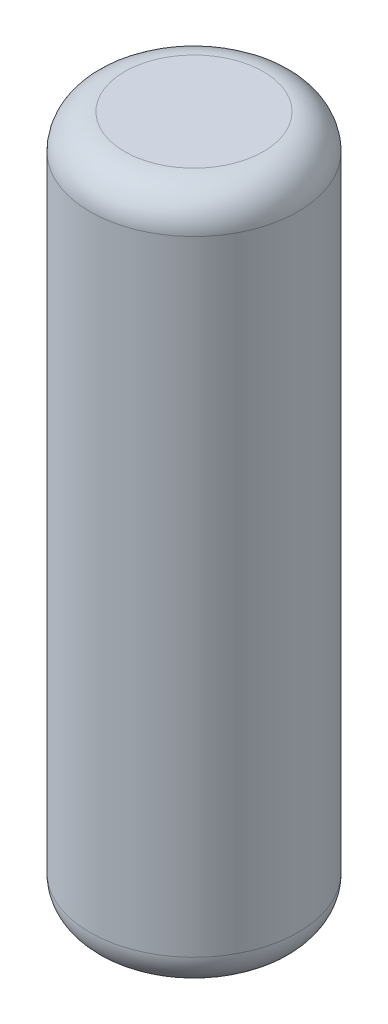
SolidWorks part; units mm, degrees
material "Cast Alloy Steel"
ref_plane "Front Plane" through (0, 0, 0) normal (0, 0, 1) x (1, 0, 0)
ref_plane "Top Plane" through (0, 0, 0) normal (0, 1, 0) x (1, 0, 0)
ref_plane "Right Plane" through (0, 0, 0) normal (1, 0, 0) x (0, 0, -1)
sketch "Sketch1" plane through (0, 0, 0) normal (0, 1, 0) x (1, 0, 0)
  circle A0 centre (0, 0) radius 30
  dimension "D1" = 60
extrude "Boss-Extrude1" add sketch "Sketch1" along normal blind 200
fillet "Fillet1" radius 10 2 edges at (0, 0, 30) (0, 200, 30)
